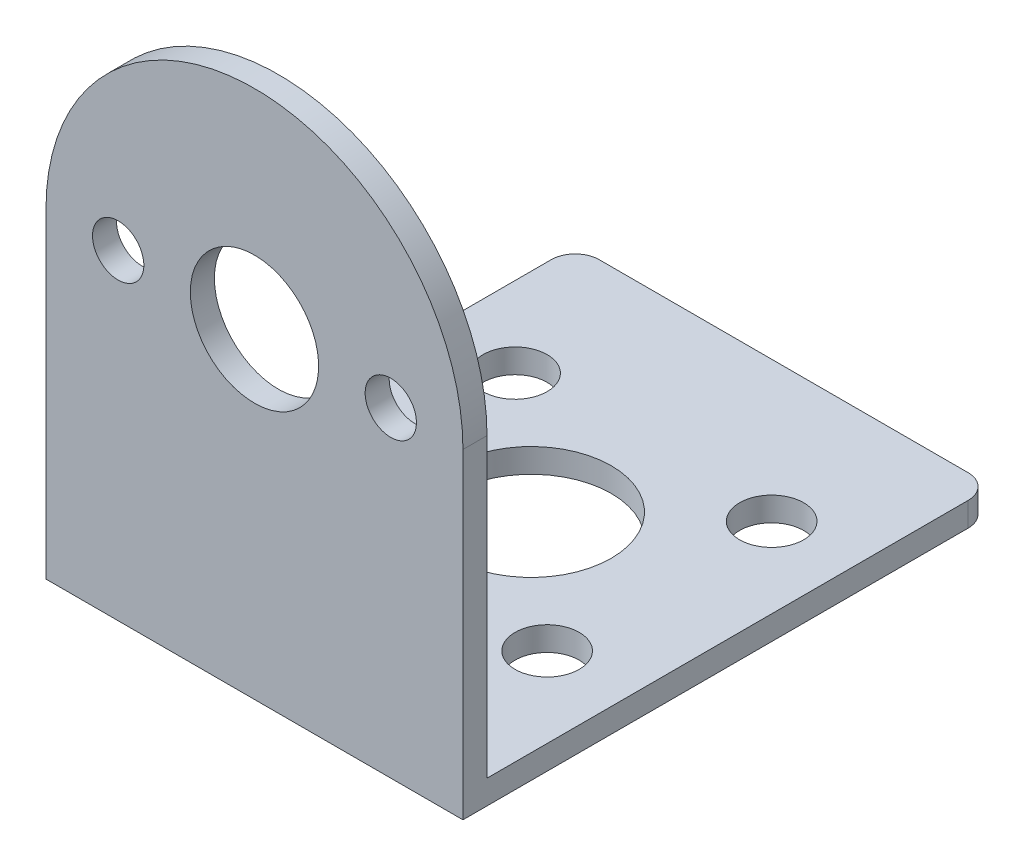
SolidWorks part; units mm, degrees
ref_plane "Front Plane" through (0, 0, 0) normal (0, 0, 1) x (1, 0, 0)
ref_plane "Top Plane" through (0, 0, 0) normal (0, 1, 0) x (1, 0, 0)
ref_plane "Right Plane" through (0, 0, 0) normal (1, 0, 0) x (0, 0, -1)
sketch "Sketch1" plane through (0, 0, 0) normal (0, 0, 1) x (1, 0, 0)
  line L1 (0, 0) -> (26, 0)
  line L2 (0, 0) -> (0, 20)
  line L4 (26, 0) -> (26, 20)
  arc A1 (26, 20) -> (0, 20) centre (13, 20) ccw
extrude "Boss-Extrude1" add sketch "Sketch1" along normal blind 1.5
sketch "Sketch2" plane through (0, 0, 0) normal (0, 0, -1) x (-1, 0, 0)
  circle A1 centre (-13, 20) radius 4
  circle A2 centre (-21.5, 20) radius 1.6
  circle A3 centre (-4.5, 20) radius 1.6
extrude "Cut-Extrude1" cut sketch "Sketch2" against normal through all
sketch "Sketch3" plane through (0, 0, 0) normal (0, 0, -1) x (-1, 0, 0)
  line L0 (0, 20) -> (0, 0) construction
  line L1 (-26, 0) -> (0, 0)
  line L2 (-26, 0) -> (-26, 1.5)
  line L3 (-26, 1.5) -> (0, 1.5)
  line L4 (0, 0) -> (0, 1.5)
extrude "Boss-Extrude4" add sketch "Sketch3" along normal blind 31.5
sketch "Sketch4" plane through (0, 0, 0) normal (0, -1, 0) x (1, 0, 0)
  circle A0 centre (13, -15.75) radius 5
  circle A1 centre (5, -8.75) radius 2
  circle A2 centre (21, -8.75) radius 2
  circle A3 centre (21, -22.75) radius 2
  circle A4 centre (5, -22.75) radius 2
extrude "Cut-Extrude2" cut sketch "Sketch4" against normal through all
fillet "Fillet1" radius 1.5 2 edges at (26, 0.75, -31.5) (0, 0.75, -31.5)
